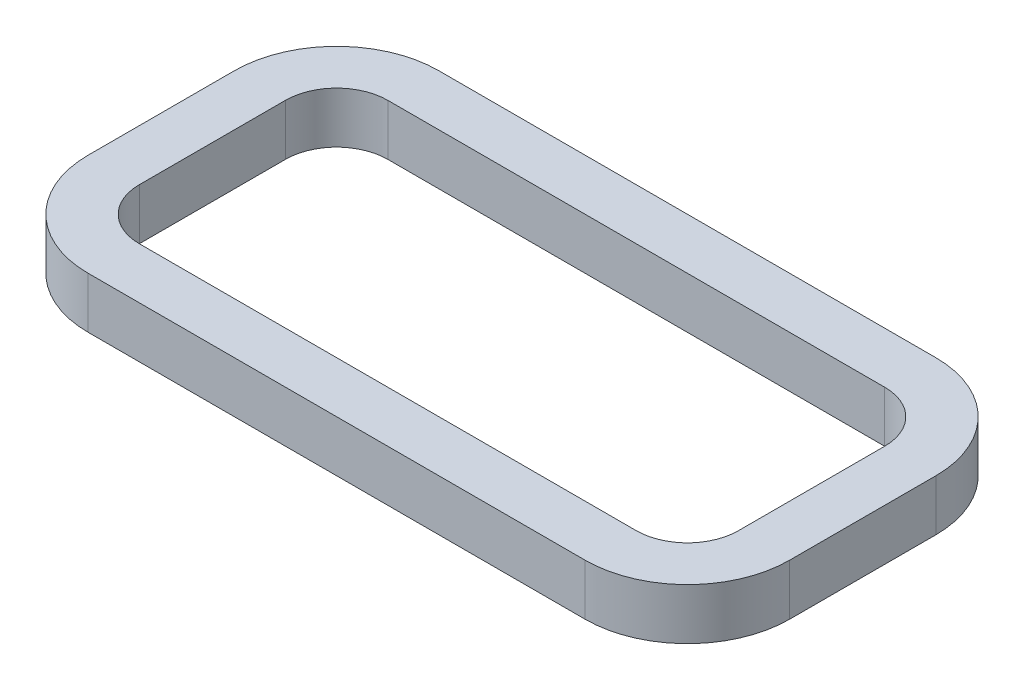
SolidWorks part; units mm, degrees
ref_plane "Front Plane" through (0, 0, 0) normal (0, 0, 1) x (1, 0, 0)
ref_plane "Top Plane" through (0, 0, 0) normal (0, 1, 0) x (1, 0, 0)
ref_plane "Right Plane" through (0, 0, 0) normal (1, 0, 0) x (0, 0, -1)
sketch "Sketch1" plane through (0, 0, 0) normal (0, 1, 0) x (1, 0, 0)
  line L1 (-107.95, 53.975) -> (107.95, 53.975)
  line L2 (-130.175, 31.75) -> (-130.175, -31.75)
  line L3 (-107.95, -53.975) -> (107.95, -53.975)
  line L4 (130.175, 31.75) -> (130.175, -31.75)
  line L5 (-130.175, 53.975) -> (130.175, -53.975) construction
  line L6 (-130.175, -53.975) -> (130.175, 53.975) construction
  arc A0 (107.95, 53.975) -> (130.175, 31.75) centre (107.95, 31.75) cw
  arc A1 (107.95, -53.975) -> (130.175, -31.75) centre (107.95, -31.75) ccw
  arc A2 (-130.175, -31.75) -> (-107.95, -53.975) centre (-107.95, -31.75) ccw
  arc A3 (-107.95, 53.975) -> (-130.175, 31.75) centre (-107.95, 31.75) ccw
  point P0 (0, 0)
  dimension "D3" = 22.225
  dimension "D1" = 107.95
  dimension "D2" = 260.35
extrude "Extrude-Thin1" add sketch "Sketch1" along normal blind 22.225 thin thin type one direction wall 22.225
